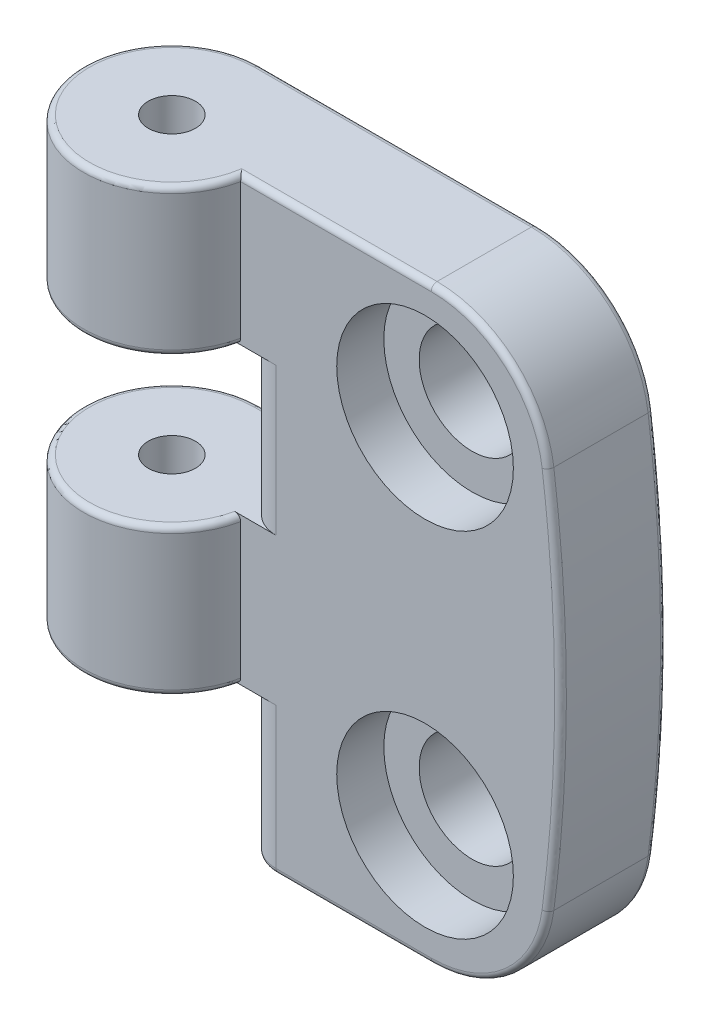
SolidWorks part; units mm, degrees
material "POM Acetal Copolymer"
ref_plane "Plan de face" through (0, 0, 0) normal (0, 0, 1) x (1, 0, 0)
ref_plane "Plan de dessus" through (0, 0, 0) normal (0, 1, 0) x (1, 0, 0)
ref_plane "Plan de droite" through (0, 0, 0) normal (1, 0, 0) x (0, 0, -1)
sketch "Sketch1" plane through (0, 0, 0) normal (0, 0, 1) x (1, 0, 0)
  line L1 (0, 0) -> (42, 0)
  line L2 (0, 0) -> (0, 50)
  line L3 (0, 50) -> (42, 50)
  line L4 (42, 0) -> (42, 50)
  dimension "D1" = 42
  dimension "D2" = 50
extrude "Boss-Extrude1" add sketch "Sketch1" along normal blind 15
sketch "Sketch2" plane through (0, 0, 0) normal (0, -1, 0) x (1, 0, 0)
  line L0 (0, 15) -> (0, 0) construction
  line L2 (42, 0) -> (7.5, 0)
  line L3 (42, 0) -> (42, 9)
  line L4 (42, 9) -> (14.8485, 9)
  arc A0 (14.8485, 9) -> (7.5, 0) centre (7.5, 7.5) ccw
  circle A1 centre (7.5, 7.5) radius 2
  dimension "D1" = 9
  dimension "D2" = 4
extrude "Cut-Extrude1" cut sketch "Sketch2" against normal through all flip side to cut
sketch "Sketch3" plane through (0, 0, 9) normal (0, 0, 1) x (1, 0, 0)
  line L0 (42, 50) -> (14.8485, 50) construction
  line L1 (42, 50) -> (42, 0) construction
  line L2 (42, 0) -> (14.8485, 0) construction
  line L4 (39.4975, 50) -> (57.0348, 50)
  line L6 (39.4975, 0) -> (57.0348, 0)
  line L7 (57.0348, 50) -> (57.0348, 0)
  spline S0 degree 2 poles (39.4975, 50) (44.5025, 25) (39.4975, 0) knots 0 0 0 1 1 1
extrude "Cut-Extrude2" cut sketch "Sketch3" against normal blind 15
fillet "Fillet1" radius 10 2 edges at (39.4975, 50, 4.5) (39.4975, 0, 4.5)
hole_wizard "CBORE for M8 Hex Socket Head Cap Screw1" positions "Sketch4" profile "Sketch5" counterbore size "M8" standard "ISO"
sketch "Sketch4" plane through (0, 0, 9) normal (0, 0, 1) x (1, 0, 0)
  line L0 (31.021, 50) -> (14.8485, 50) construction
  line L2 (14.8485, 50) -> (14.8485, 0) construction
  point P0 (30.4985, 10)
  point P2 (30.4985, 40)
  dimension "D1" = 30
  dimension "D2" = 10
  dimension "D3" = 15.65
sketch "Sketch5" plane through (30.4985, 10, 9) normal (1, 0, 0) x (0, -1, 0)
  line L0 (0, 0) -> (0, 17.7039)
  line L1 (0, 17.7039) -> (4.5, 15)
  line L2 (4.5, 15) -> (4.5, 4)
  line L3 (4.5, 4) -> (7.5, 4)
  line L4 (7.5, 4) -> (7.5, 0)
  line L5 (7.5, 0) -> (0, 0)
  line L10 (0, 17.7039) -> (-4.5, 15) construction
  line L11 (0, -6.35) -> (0, 107.95) construction
  dimension "Hole Dia." = 9
  dimension "Hole Depth" = 15
  dimension "C'Bore Dia." = 15
  dimension "C'Bore Depth" = 4
  dimension "Drill Angle" = 118
sketch "Sketch6" plane through (0, 0, 9) normal (0, 0, 1) x (1, 0, 0)
  line L0 (14.8485, 50) -> (14.8485, 0) construction
  line L1 (0, 0) -> (14.8485, 0)
  line L2 (0, 0) -> (0, 12.5)
  line L3 (0, 12.5) -> (14.8485, 12.5)
  line L4 (14.8485, 0) -> (14.8485, 12.5)
  line L5 (0, 50) -> (0, 0) construction
  line L6 (0, 25) -> (14.8485, 25)
  line L7 (0, 25) -> (0, 37.5)
  line L8 (0, 37.5) -> (14.8485, 37.5)
  line L9 (14.8485, 25) -> (14.8485, 37.5)
  dimension "D1" = 12.5
  dimension "D2" = 12.5
  dimension "D3" = 12.5
extrude "Cut-Extrude3" cut sketch "Sketch6" against normal through all both and the other way through all
fillet "Fillet2" radius 3 4 edges at (14.8485, 31.25, 0) (14.8485, 31.25, 9) (14.8485, 6.25, 0) (14.8485, 6.25, 9)
fillet "Fillet3" radius 0.5 20 edges at (12.6742, 25, 0) (12.6742, 12.5, 0) (22.9348, 50, 9) (37.6188, 47.5146, 9) (37.6188, 2.4854, 9) (24.4348, 0, 9) (15.7271, 0, 8.1213) (14.8485, 0, 4.5) (15.7271, 0, 0.8787) (24.4348, 0, 0) (37.6188, 2.4854, 0) (37.6188, 47.5146, 0) (19.2605, 50, 0) (12.6742, 37.5, 0) (1.6905, 25, 12.2434) (1.6905, 12.5, 12.2434) (1.6905, 50, 12.2434) (1.6905, 37.5, 12.2434)
